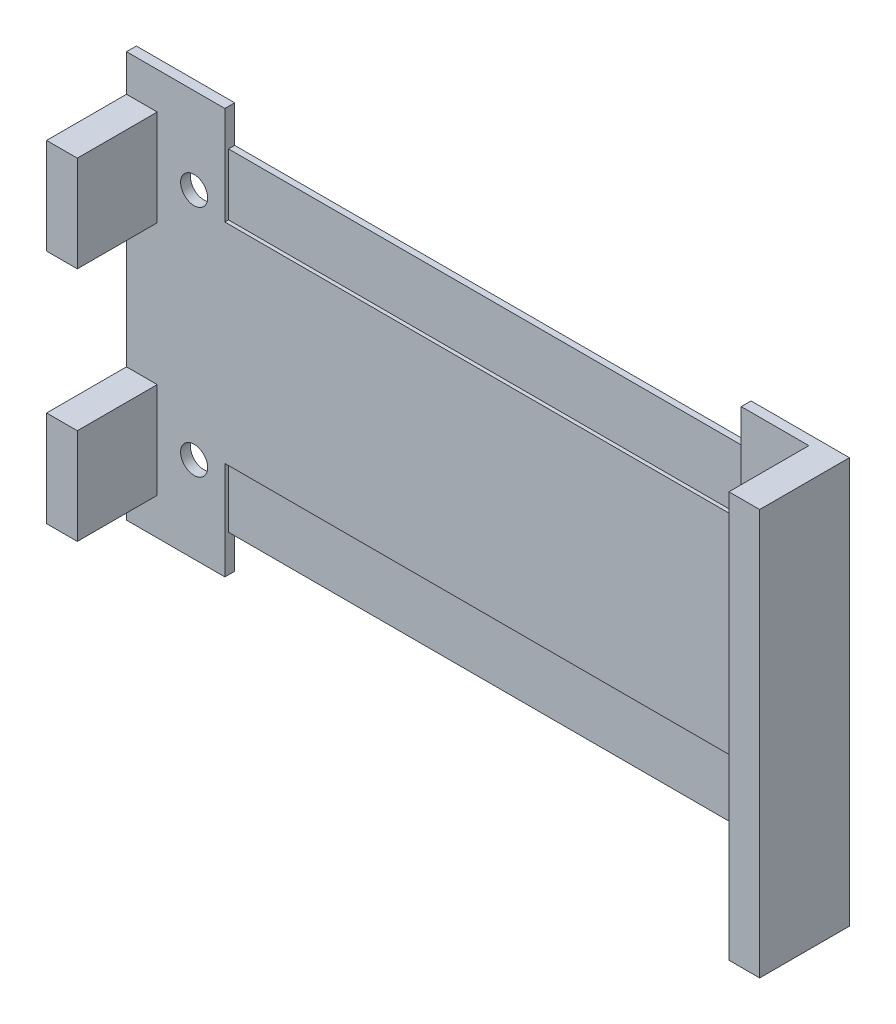
SolidWorks part; units mm, degrees
ref_plane "Front Plane" through (0, 0, 0) normal (0, 0, 1) x (1, 0, 0)
ref_plane "Top Plane" through (0, 0, 0) normal (0, 1, 0) x (1, 0, 0)
ref_plane "Right Plane" through (0, 0, 0) normal (1, 0, 0) x (0, 0, -1)
ref_plane "Plane1" through (0, 0, -2.3) normal (0, 0, 1) x (1, 0, 0)
sketch "Sketch1" plane through (0, 0, -2.3) normal (0, 0, 1) x (1, 0, 0)
  line L0 (52, -5) -> (55, -5)
  line L1 (0, 28) -> (5, 28)
  line L2 (0, 28) -> (0, -5) construction
  line L3 (0, -5) -> (5, -5)
  line L4 (52, 28) -> (52, -5) construction
  line L5 (52, 0) -> (52, 23) construction
  line L6 (0, 0) -> (52, 0) construction
  line L7 (55, -5) -> (55, 28)
  line L8 (47, -5) -> (47, 3)
  line L9 (47, 3) -> (5, 3)
  line L10 (5, -5) -> (5, 3)
  line L11 (55, 28) -> (52, 28)
  line L12 (5, 28) -> (5, 20)
  line L13 (5, 20) -> (47, 20)
  line L14 (47, 28) -> (47, 20)
  line L15 (52, 23) -> (0, 23) construction
  line L16 (47, -5) -> (52, -5)
  line L17 (47, 28) -> (52, 28)
  line L18 (0, -5) -> (-3, -5)
  line L19 (-3, -5) -> (-3, 28)
  line L20 (-3, 28) -> (0, 28)
  circle A0 centre (49.5, 2) radius 1.1
  circle A1 centre (49.5, 21) radius 1.1
  circle A2 centre (2.5, 2) radius 1.1
  circle A3 centre (2.5, 21) radius 1.1
  dimension "D6" = 2.2
  dimension "D1" = 5
  dimension "D2" = 5
  dimension "D3" = 8
  dimension "D4" = 8
  dimension "D5" = 5
  dimension "D7" = 3
  dimension "D8" = 3
extrude "Boss-Extrude1" add sketch "Sketch1" along normal up to vertex (0.8 mm away)
sketch "Sketch2" plane through (0, 0, -2.3) normal (0, 0, 1) x (1, 0, 0)
  line L1 (5, -5) -> (5, 3) construction
  line L2 (5, -2) -> (47, -2)
  line L3 (5, -2) -> (5, 25)
  line L4 (5, 25) -> (47, 25)
  line L6 (47, -2) -> (47, 25)
  line L7 (47, 28) -> (47, 20) construction
  line L10 (5, 20) -> (5, 28) construction
  line L11 (-3, -5) -> (5, -5) construction
  line L12 (5, 28) -> (-3, 28) construction
  dimension "D1" = 3
  dimension "D2" = 3
extrude "Boss-Extrude2" add sketch "Sketch2" along normal blind 0.5
sketch "Sketch3" plane through (0, 0, -1.5) normal (0, 0, 1) x (1, 0, 0)
  line L0 (55, 28) -> (47, 28) construction
  line L1 (55, -5) -> (52.5, -5)
  line L2 (55, -5) -> (55, 28)
  line L3 (55, 28) -> (52.5, 28)
  line L4 (52.5, -5) -> (52.5, 28)
  line L5 (52, 0) -> (52, 23) construction
  line L6 (-3, 28) -> (-3, -5) construction
  line L7 (-3, -2) -> (-0.5, -2)
  line L8 (-3, -2) -> (-3, 5.8)
  line L9 (-3, 5.8) -> (-0.5, 5.8)
  line L10 (-0.5, -2) -> (-0.5, 5.8)
  line L11 (5, -2) -> (47, -2) construction
  line L12 (-3, 17.2) -> (-0.5, 17.2)
  line L13 (-3, 17.2) -> (-3, 25)
  line L14 (-3, 25) -> (-0.5, 25)
  line L15 (-0.5, 17.2) -> (-0.5, 25)
  line L16 (47, 25) -> (5, 25) construction
  line L17 (0, 3.5) -> (0, 0) construction
  line L18 (-3.1, 6.8) -> (-1.1, 6.8) construction
  line L19 (-3.1, 16.2) -> (-1.1, 16.2) construction
  dimension "D1" = 0.5
  dimension "D2" = 0.5
  dimension "D3" = 1
  dimension "D4" = 1
extrude "Boss-Extrude3" add sketch "Sketch3" along normal up to vertex (6.5 mm away)
